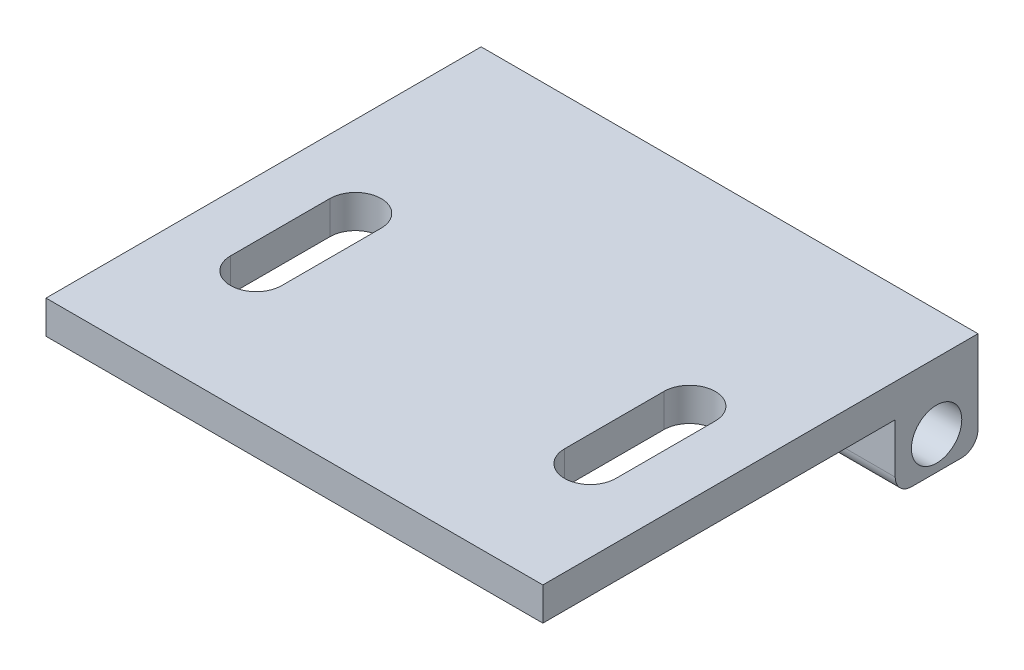
SolidWorks part; units mm, degrees
ref_plane "Ebene vorne" through (0, 0, 0) normal (0, 0, 1) x (1, 0, 0)
ref_plane "Ebene oben" through (0, 0, 0) normal (0, 1, 0) x (1, 0, 0)
ref_plane "Ebene rechts" through (0, 0, 0) normal (1, 0, 0) x (0, 0, -1)
sketch "Skizze5" plane through (0, 0, 0) normal (1, 0, 0) x (0, 0, -1)
  line L0 (-11.5556, 6.1111) -> (-11.5556, 4.1111)
  line L1 (-11.5556, 4.1111) -> (9.7179, 4.1111)
  line L2 (14.7179, 1.1111) -> (14.7179, 6.1111)
  line L3 (13.7179, 0.1111) -> (10.7179, 0.1111)
  line L5 (14.2179, 6.1111) -> (-11.5556, 6.1111)
  line L8 (9.7179, 4.1111) -> (9.7179, 1.1111)
  line L10 (14.2179, 6.1111) -> (14.7179, 6.1111)
  circle A0 centre (12.2179, 2.1111) radius 1.52
  arc A1 (14.7179, 1.1111) -> (13.7179, 0.1111) centre (13.7179, 1.1111) cw
  arc A2 (9.7179, 1.1111) -> (10.7179, 0.1111) centre (10.7179, 1.1111) ccw
  dimension "D1" = 1
extrude "Aufsatz-Linear austragen3" add sketch "Skizze5" along normal blind 30
sketch "Skizze6" plane through (0, 6.1111, 0) normal (0, 1, 0) x (1, 0, 0)
  line L0 (34.9144, -0.2821) -> (-5.0856, -0.2821) construction
  line L1 (25.0856, -3.7821) -> (25.0856, 2.2179) construction
  line L2 (15, -11.5556) -> (15, 8.3627) construction
  line L3 (30, -11.5556) -> (0, -11.5556) construction
  line L4 (34.9144, 2.2179) -> (-5.0856, 2.2179) construction
  line L5 (34.9144, -3.7821) -> (-5.0856, -3.7821) construction
  line L6 (4.9144, -3.7821) -> (4.9144, 2.2179) construction
  line L7 (3.3644, -3.7821) -> (3.3644, 2.2179)
  line L8 (6.4644, -3.7821) -> (6.4644, 2.2179)
  line L9 (26.6356, -3.7821) -> (26.6356, 2.2179)
  line L10 (23.5356, -3.7821) -> (23.5356, 2.2179)
  arc A0 (3.3644, -3.7821) -> (6.4644, -3.7821) centre (4.9144, -3.7821) ccw
  arc A1 (6.4644, 2.2179) -> (3.3644, 2.2179) centre (4.9144, 2.2179) ccw
  arc A2 (26.6356, -3.7821) -> (23.5356, -3.7821) centre (25.0856, -3.7821) cw
  arc A3 (23.5356, 2.2179) -> (26.6356, 2.2179) centre (25.0856, 2.2179) cw
  point P17 (4.9144, -0.7821)
  point P22 (25.0856, -0.7821)
extrude "Schnitt-Linear austragen1" cut sketch "Skizze6" against normal blind 10
